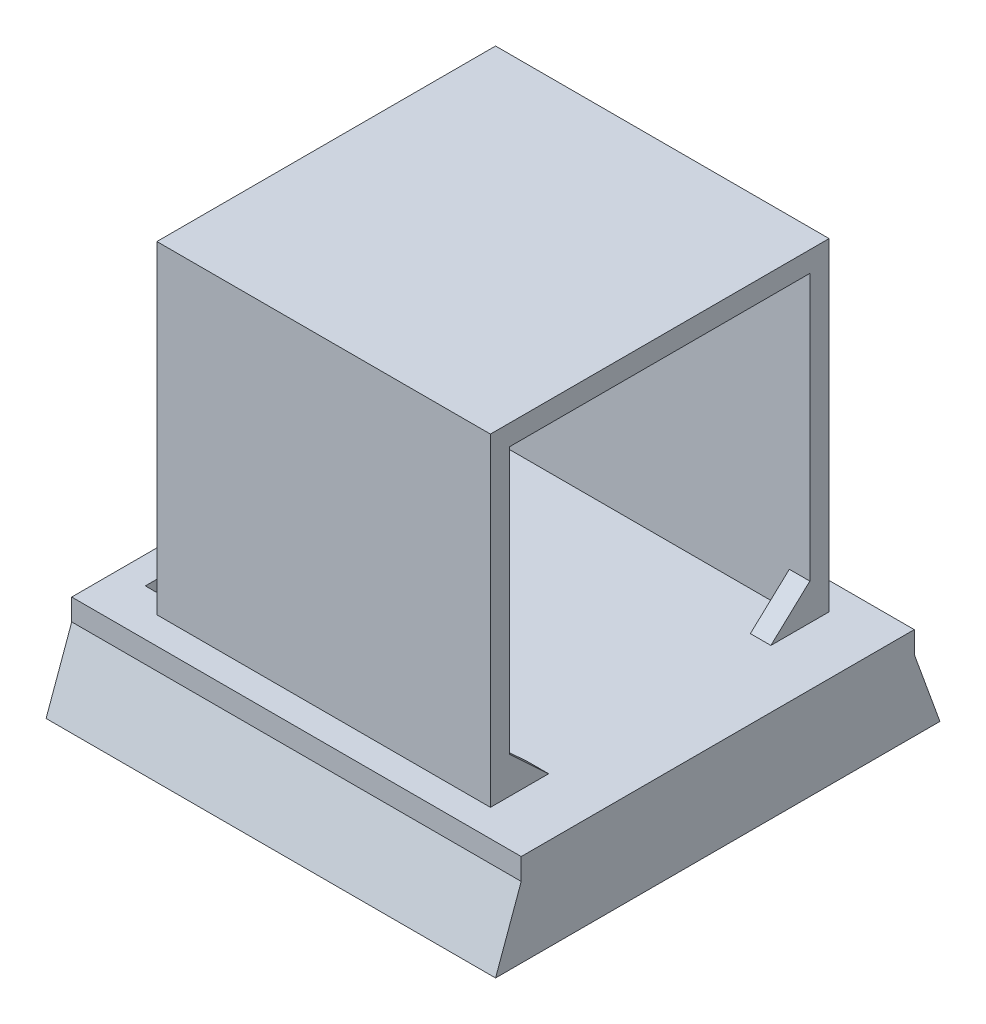
SolidWorks part; units mm, degrees
ref_plane "Front Plane" through (0, 0, 0) normal (0, 0, 1) x (1, 0, 0)
ref_plane "Top Plane" through (0, 0, 0) normal (0, 1, 0) x (1, 0, 0)
ref_plane "Right Plane" through (0, 0, 0) normal (1, 0, 0) x (0, 0, -1)
sketch "Sketch1" plane through (0, 0, 0) normal (0, 0, 1) x (1, 0, 0)
  line L0 (-8.45, 8.1683) -> (8.45, 8.1683) construction
  line L1 (-15, 14.5) -> (15, 14.5)
  line L2 (-15, 14.5) -> (-15, -14.5)
  line L3 (-15, -14.5) -> (15, -14.5)
  line L4 (15, 14.5) -> (15, -14.5)
  line L5 (-15, 14.5) -> (15, -14.5) construction
  line L6 (-15, -14.5) -> (15, 14.5) construction
  circle A0 centre (-8.45, 8.1683) radius 1.75
  circle A1 centre (8.1683, 8.45) radius 1.75
  circle A2 centre (8.45, -8.1683) radius 1.75
  circle A3 centre (-8.1683, -8.45) radius 1.75
  point P0 (0, 0)
  point P18 (0, 0)
  dimension "D4" = 3.5
  dimension "D1" = 30
  dimension "D2" = 29
  dimension "D3" = 16.9
  dimension "D5" = 4
extrude "Boss-Extrude1" add sketch "Sketch1" along normal blind 2
sketch "Sketch2" plane through (0, -14.5, 0) normal (0, -1, 0) x (1, 0, 0)
  line L0 (-21.9, 0) -> (21.9, 0)
  line L2 (-21.9, 0) -> (-21.9, 38.3)
  line L3 (-21.9, 38.3) -> (21.9, 38.3)
  line L4 (21.9, 38.3) -> (21.9, 0)
  point P4 (0, 0)
  dimension "D1" = 43.8
  dimension "D2" = 38.3
extrude "Boss-Extrude3" add sketch "Sketch2" along normal blind 9
sketch "Sketch3" plane through (-21.9, 0, 0) normal (-1, 0, 0) x (0, 0, 1)
  line L0 (0, -23.5) -> (-2.5, -23.5)
  line L1 (19.15, -23.5) -> (19.15, -27.7431) construction
  line L2 (38.3, -23.5) -> (0, -23.5) construction
  line L3 (38.3, -23.5) -> (40.8, -23.5)
  line L4 (0, -23.5) -> (0, -16.6)
  line L5 (0, -23.5) -> (0, -14.5) construction
  line L6 (0, -16.6) -> (-2.5, -23.5)
  line L7 (38.3, -23.5) -> (38.3, -16.6)
  line L8 (38.3, -16.6) -> (40.8, -23.5)
  dimension "D1" = 2.5
  dimension "D2" = 6.9
extrude "Boss-Extrude4" add sketch "Sketch3" against normal up to vertex (43.8 mm away)
sketch "Sketch11" plane through (0, 0, 2) normal (0, 0, 1) x (1, 0, 0)
  line L0 (-14.1526, -14.5) -> (14.25, -14.5) construction
  line L1 (-15, -14.5) -> (15, -14.5) construction
ref_plane "Plane1" through (0, 0, 19.15) normal (0, 0, -1) x (-1, 0, 0)
ref_plane "Plane2" through (0, 0, 4.65) normal (0, 0, -1) x (-1, 0, 0)
sketch "Sketch15" plane through (0, 0, 4.65) normal (0, 0, -1) x (-1, 0, 0)
  line L1 (15, 14.5) -> (15, -14.5) construction
  line L2 (-15, 14.5) -> (-15, -14.5) construction
  line L3 (0, -14.5) -> (0, -6.3378) construction
  line L8 (-16.25, -14.5) -> (16.25, -14.5)
  line L9 (21.9, -14.5) -> (15, -14.5) construction
  line L10 (-16.25, -14.5) -> (-16.25, 17)
  line L11 (-16.25, 17) -> (16.25, 17)
  line L12 (16.25, 17) -> (16.25, -14.5)
  point P12 (0, -14.5)
  dimension "D1" = 30
  dimension "D2" = 32.5
  dimension "D3" = 31.5
sketch "Sketch16" plane through (0, 0, 0) normal (1, 0, 0) x (0, 0, -1)
  line L1 (-2, 14.5) -> (0, 14.5)
  line L2 (-2, 14.5) -> (-2, -14.5)
  line L3 (-2, -14.5) -> (0, -14.5)
  line L4 (0, 14.5) -> (0, -14.5)
extrude "Cut-Extrude1" cut sketch "Sketch16" against normal mid plane 53
extrude "Boss-Extrude5" add sketch "Sketch15" against normal blind 31 and the other way blind 2
sketch "Sketch20" plane through (0, 0, 0) normal (1, 0, 0) x (0, 0, -1)
  line L0 (-33.775, -14.5) -> (-33.775, 15)
  line L1 (-2.65, -14.5) -> (-35.65, -14.5) construction
  line L2 (-33.775, 15) -> (-4.525, 15)
  line L3 (-19.15, 15) -> (-19.15, -14.5) construction
  line L4 (0, -14.5) -> (-38.3, -14.5) construction
  line L5 (-4.525, -14.5) -> (-33.775, -14.5)
  line L6 (-4.525, -14.5) -> (-4.525, 15)
  dimension "D1" = 29.25
  dimension "D2" = 29.5
extrude "Cut-Extrude2" cut sketch "Sketch20" against normal through all both and the other way through all contours L6 L2 L0 L5
sketch "Sketch21" plane through (16.25, 0, 0) normal (1, 0, 0) x (0, 0, -1)
  line L0 (-35.65, -10.971) -> (-33.775, -10.971)
  line L1 (-35.65, 17) -> (-35.65, -14.5) construction
  line L2 (-33.775, 15) -> (-33.775, -14.5) construction
  line L3 (-33.775, -10.971) -> (-29.9767, -14.5)
  line L4 (0, -14.5) -> (-38.3, -14.5) construction
  line L5 (-29.9767, -14.5) -> (-35.65, -14.5)
  line L6 (-35.65, -14.5) -> (-35.65, -10.971)
  line L7 (-19.15, -14.5) -> (-19.15, -8.9024) construction
  line L8 (-19.15, -17.105) -> (-19.15, 17.105) construction
  line L9 (-4.525, -10.971) -> (-8.3233, -14.5)
  line L10 (-8.3233, -14.5) -> (-2.65, -14.5)
  line L11 (-2.65, -14.5) -> (-2.65, -10.971)
  line L12 (-2.65, -10.971) -> (-4.525, -10.971)
extrude "Boss-Extrude6" add sketch "Sketch21" against normal blind 2
sketch "Sketch22" plane through (0, -14.5, 0) normal (0, 1, 0) x (1, 0, 0)
  line L0 (-16.25, -2.65) -> (-16.25, -35.65) construction
  line L1 (-16.25, -4.525) -> (-19.25, -4.525)
  line L2 (-16.25, -4.525) -> (-16.25, -33.775)
  line L3 (-16.25, -19.15) -> (-19.25, -19.15) construction
  line L4 (-19.25, -4.525) -> (-19.25, -33.775)
  line L5 (-16.25, -2.65) -> (-16.25, -4.525) construction
  line L6 (17.105, -19.15) -> (-17.105, -19.15) construction
  line L7 (-16.25, -33.775) -> (-19.25, -33.775)
  dimension "D1" = 29.25
  dimension "D2" = 3
extrude "Cut-Extrude3" cut sketch "Sketch22" against normal blind 2
